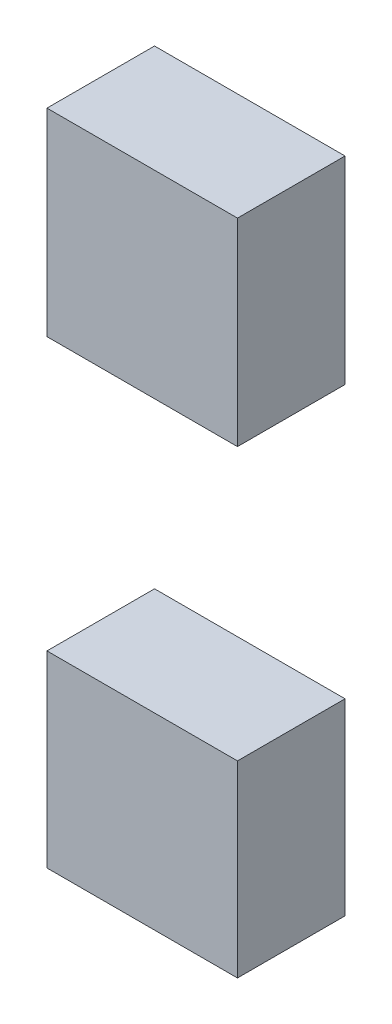
SolidWorks part; units mm, degrees
ref_plane "Front Plane" through (0, 0, 0) normal (0, 0, 1) x (1, 0, 0)
ref_plane "Top Plane" through (0, 0, 0) normal (0, 1, 0) x (1, 0, 0)
ref_plane "Right Plane" through (0, 0, 0) normal (1, 0, 0) x (0, 0, -1)
sketch "Sketch1" plane through (0, 0, 0) normal (0, 0, 1) x (1, 0, 0)
  line L0 (0, 21.6204) -> (0, -21.6204) construction
  line L1 (-8.8552, 12.4202) -> (8.8552, 12.4202)
  line L2 (-8.8552, 12.4202) -> (-8.8552, 30.8205)
  line L3 (-8.8552, 30.8205) -> (8.8552, 30.8205)
  line L4 (8.8552, 12.4202) -> (8.8552, 30.8205)
  line L5 (-8.8552, 12.4202) -> (8.8552, 30.8205) construction
  line L6 (-8.8552, 30.8205) -> (8.8552, 12.4202) construction
  line L7 (-8.8552, -30.3605) -> (8.8552, -30.3605)
  line L8 (-8.8552, -30.3605) -> (-8.8552, -12.8802)
  line L9 (-8.8552, -12.8802) -> (8.8552, -12.8802)
  line L10 (8.8552, -30.3605) -> (8.8552, -12.8802)
  line L11 (-8.8552, -30.3605) -> (8.8552, -12.8802) construction
  line L12 (-8.8552, -12.8802) -> (8.8552, -30.3605) construction
  point P0 (0, 21.6204)
  point P5 (0, -21.6204)
extrude "Boss-Extrude1" add sketch "Sketch1" along normal blind 10
